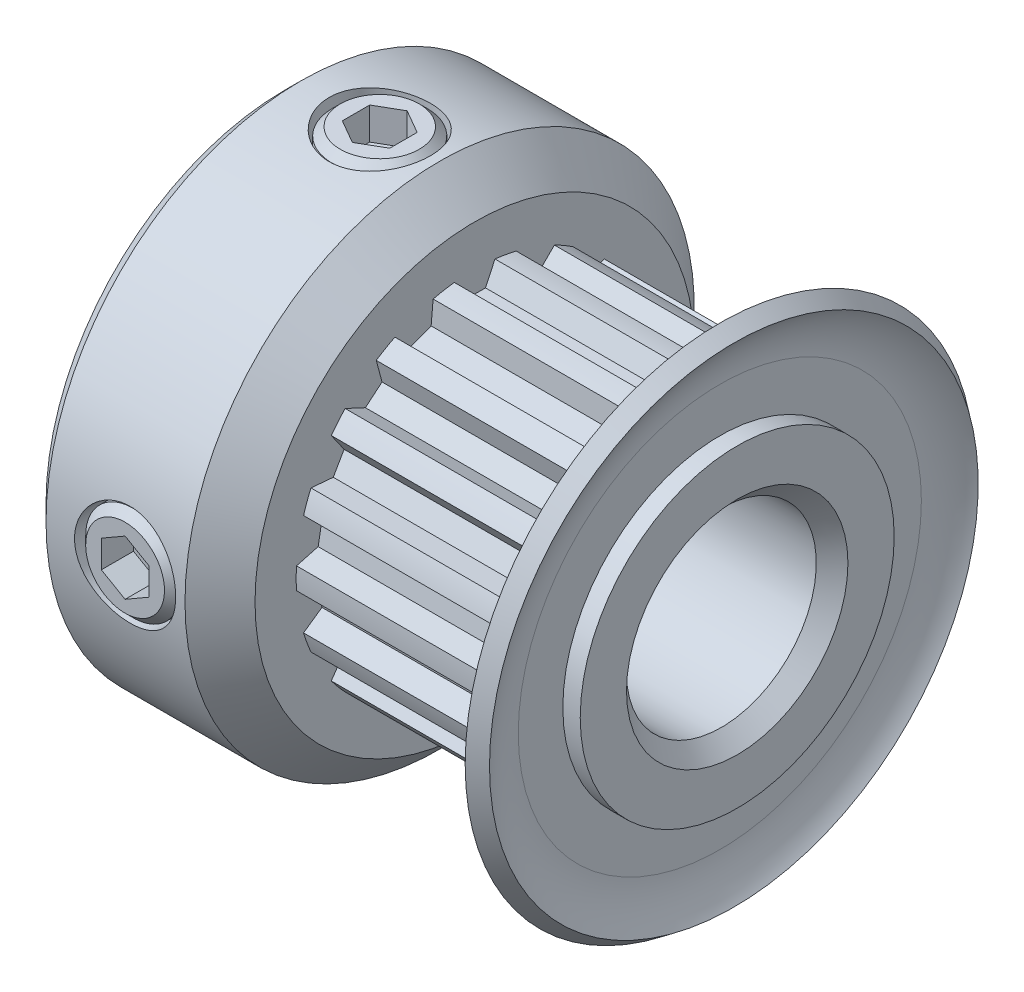
SolidWorks part; units mm, degrees
ref_plane "Front Plane" through (0, 0, 0) normal (0, 0, 1) x (1, 0, 0)
ref_plane "Top Plane" through (0, 0, 0) normal (0, 1, 0) x (1, 0, 0)
ref_plane "Right Plane" through (0, 0, 0) normal (1, 0, 0) x (0, 0, -1)
sketch "Sketch2" plane through (0, 0, 0) normal (1, 0, 0) x (0, 0, -1)
  line L3 (0, 0) -> (0, 4.9745) construction
  line L6 (0, -5.4825) -> (0, -5.8) construction
  line L7 (-0.5715, 5.4526) -> (-0.343, 4.9627)
  line L8 (0.5715, 5.4526) -> (0.343, 4.9627)
  line L9 (-0.5715, 5.4526) -> (-0.6423, 5.6046)
  line L10 (0.5715, 5.4526) -> (0.6423, 5.6046)
  line L12 (-0.343, 4.9627) -> (0.343, 4.9627)
  line L14 (0, 5.4825) -> (0, 5.8) construction
  line L15 (0, 0) -> (0, -1.143) construction
  circle A0 centre (0, 0) radius 5.8 construction
  circle A1 centre (0, 0) radius 4.9745 construction
  circle A2 centre (0, 0) radius 5.4825 construction
  arc A7 (0.6423, 5.6046) -> (-0.6423, 5.6046) centre (0, 0) ccw
  point P5 (0, 5.6412)
  dimension "D3" = 0.3175
  dimension "D1" = 50
sketch "Sketch1" plane through (0, 0, 0) normal (0, 0, 1) x (1, 0, 0)
  line L0 (-7.15, 0) -> (7.15, 0) construction
  line L1 (-7.15, 3) -> (7.15, 3)
  line L2 (-7.15, 3) -> (-7.15, 8.05)
  line L3 (-7.15, 8.05) -> (-2.257, 8.05)
  line L4 (-2.257, 8.05) -> (-1.15, 6.943)
  line L5 (-1.15, 6.943) -> (-1.15, 5.8)
  line L6 (-1.15, 5.8) -> (6.05, 5.8)
  line L7 (6.05, 5.8) -> (6.05, 6.3715)
  line L8 (6.05, 5.8) -> (7.15, 5.8) construction
  line L9 (6.6, 8.05) -> (7.15, 8.05)
  line L10 (7.15, 8.05) -> (7.15, 3)
  line L11 (6.6, 5.8) -> (6.6, 8.05) construction
  line L12 (-4.7035, 8.05) -> (-4.7035, 3) construction
  arc A0 (6.05, 6.3715) -> (6.6, 8.05) centre (8.8862, 6.3715) cw
  dimension "Bore Size" = 6
  dimension "Overall Width" = 14.3
  dimension "Inside Width" = 7.2
  dimension "Outside Width" = 8.3
  dimension "Hub Dia" = 16.1
  dimension "OD" = 16.1
  dimension "D1" = 45
  dimension "D2" = 11.6
  dimension "D3" = 1.143
  dimension "D4" = 0.5715
revolve "Revolve1" add sketch "Sketch1" angle 360 mid plane about L0
sketch "Sketch4" plane through (-1.15, 0, 0) normal (1, 0, 0) x (0, 0, -1)
  circle A0 centre (0, 0) radius 5.6412
  circle A1 centre (0, 0) radius 5.8 construction
  circle A2 centre (0, 0) radius 5.8
extrude "Cut-Extrude2" cut sketch "Sketch4" along normal up to surface (7.2 mm away) up to face at (6.05, 0, 5.8)
sketch "Sketch3" plane through (-1.15, 0, 0) normal (1, 0, 0) x (0, 0, -1)
  line L2 (-0.5715, 5.4526) -> (-0.343, 4.9627) construction
  line L3 (-0.343, 4.9627) -> (0.343, 4.9627) construction
  line L4 (0.5715, 5.4526) -> (0.343, 4.9627) construction
  line L5 (-0.6423, 5.6046) -> (-0.343, 4.9627)
  line L6 (-0.343, 4.9627) -> (0.343, 4.9627)
  line L7 (0.6423, 5.6046) -> (0.343, 4.9627)
  arc A1 (0.6423, 5.6046) -> (-0.6423, 5.6046) centre (0, 0) ccw construction
  arc A2 (0.6423, 5.6046) -> (-0.6423, 5.6046) centre (0, 0) ccw
extrude "Cut-Extrude1" cut sketch "Sketch3" along normal up to surface (7.2 mm away)
pattern_circular "CirPattern1" count 18 over 360 about axis through (0, 0, 0) along (1, 0, 0) of "Cut-Extrude1"
sketch "Sketch5" plane through (0, 0, 0) normal (0, 1, 0) x (1, 0, 0)
  line L0 (-7.15, 8.05) -> (-7.15, -8.05) construction
  line L1 (6.05, 6.3715) -> (6.05, -6.3715) construction
  line L2 (7.15, 8.05) -> (7.15, -8.05) construction
  line L3 (-1.15, 6.943) -> (-1.15, -6.943) construction
  line L4 (6.05, 6.3715) -> (6.05, -6.3715) construction
  line L5 (-7.15, 0) -> (7.15, 0) construction
  line L6 (-7.15, 0) -> (7.15, 0) construction
  point P0 (6.05, 0)
  point P14 (6.05, 0)
  point P15 (-1.15, 0)
  dimension "D1" = 16.1
  dimension "D2" = 16.1
sketch "Sketch6" plane through (0, 0, 0) normal (0, 1, 0) x (1, 0, 0)
  line L0 (-7.15, 0) -> (-5.65, 0) construction
  line L1 (-7.15, 8.05) -> (-7.15, -8.05) construction
  line L2 (-1.15, 0) -> (-2.65, 0) construction
  line L3 (-1.15, -0.343) -> (-1.15, 0.343) construction
  line L4 (-5.65, 0) -> (-4.15, 0) construction
  line L5 (-4.15, 0) -> (-5.2107, -1.0607) construction
  circle A0 centre (-4.15, 0) radius 1.5 construction
  circle A1 centre (-4.15, 0) radius 1.6
  point P13 (-5.2107, -1.0607)
  dimension "D1" = 0.1
  dimension "D2" = 45
  dimension "SS Dia" = 3
extrude "Cut-Extrude3" cut sketch "Sketch6" along normal through all
sketch "Sketch7" plane through (0, 0, 0) normal (0, 0, 1) x (1, 0, 0)
  line L0 (-5.396, 8.05) -> (-4.15, 8.05)
  line L1 (-5.65, 7.796) -> (-5.65, 3.635)
  line L2 (-5.65, 3.635) -> (-5.396, 3.381)
  line L3 (-5.396, 3.381) -> (-4.15, 3.381)
  line L4 (-4.15, 3.381) -> (-4.15, 8.05) construction
  line L6 (-5.65, 7.796) -> (-5.396, 8.05)
  line L7 (-7.15, 8.05) -> (-2.257, 8.05) construction
  line L8 (-4.15, 8.05) -> (-4.15, 3.381)
  point P0 (-5.65, 8.05)
  point P4 (-5.65, 3.381)
  dimension "D2" = 0.381
revolve "Revolve2" add sketch "Sketch7" angle 360 mid plane about L4
sketch "Sketch8" plane through (0, 8.05, 0) normal (0, 1, 0) x (1, 0, 0)
  line L0 (-4.15, 0) -> (-5.65, 0) construction
  line L1 (-4.15, 0.866) -> (-4.9, 0.433)
  line L2 (-4.9, 0.433) -> (-4.9, -0.433)
  line L3 (-4.9, -0.433) -> (-4.15, -0.866)
  line L4 (-4.15, -0.866) -> (-3.4, -0.433)
  line L5 (-3.4, -0.433) -> (-3.4, 0.433)
  line L6 (-3.4, 0.433) -> (-4.15, 0.866)
  circle A0 centre (-4.15, 0) radius 0.75 construction
  point P13 (-4.9, 0)
extrude "Cut-Extrude4" cut sketch "Sketch8" against normal blind 1.016
pattern_circular "CirPattern2" count 2 over 90 about axis through (-7.15, 0, 0) along (-1, 0, 0) of "Cut-Extrude3"
pattern_circular "CirPattern3" count 2 over 90 about axis through (0, 0, 0) along (1, 0, 0) of bodies 107
chamfer "Chamfer1" distance 0.5 angle 45 3 edges at (-7.15, 0, 8.05) (-7.15, 0, 3) (7.15, 0, 3)
sketch "Sketch9" plane through (0, 0, 0) normal (0, 0, 1) x (1, 0, 0)
  line L0 (7.15, 4.9627) -> (7.15, 8.05)
  line L1 (7.15, 8.05) -> (7.15, 3) construction
  line L2 (6.6, 5.8) -> (6.6, 8.05) construction
  line L3 (6.6, 6.3715) -> (6.6, 4.9627)
  line L4 (6.6, 8.05) -> (6.7926, 8.3124)
  line L5 (6.6, 4.9627) -> (7.15, 4.9627)
  line L6 (6.6, 8.05) -> (7.0433, 7.7245)
  line L7 (6.7926, 8.3124) -> (7.15, 8.05)
  line L8 (-1.15, 4.9627) -> (7.15, 4.9627) construction
  line L9 (-7.15, 0) -> (7.15, 0) construction
  line L10 (-7.15, 0) -> (7.15, 0) construction
  arc A0 (6.6, 8.05) -> (6.05, 6.3715) centre (8.8862, 6.3715) ccw construction
  arc A3 (6.6, 6.3715) -> (7.0433, 7.7245) centre (8.8862, 6.3715) cw
revolve "Cut-Revolve1" cut sketch "Sketch9" angle 360 about L0
equation "\"D3@Sketch2\" = (\"hs@Sketch2\"-\"ht@Sketch2\")/2"
equation "\"D2@Sketch1\" = \"PD@Sketch2\""
equation "\"D3@Sketch1\" = \"hs@Sketch2\""
equation "\"D4@Sketch1\" = \"D3@Sketch1\"/2"
equation "\"D1@Sketch5\"=\"Hub Dia@Sketch1\""
equation "\"D2@Sketch5\"=\"OD@Sketch1\""
